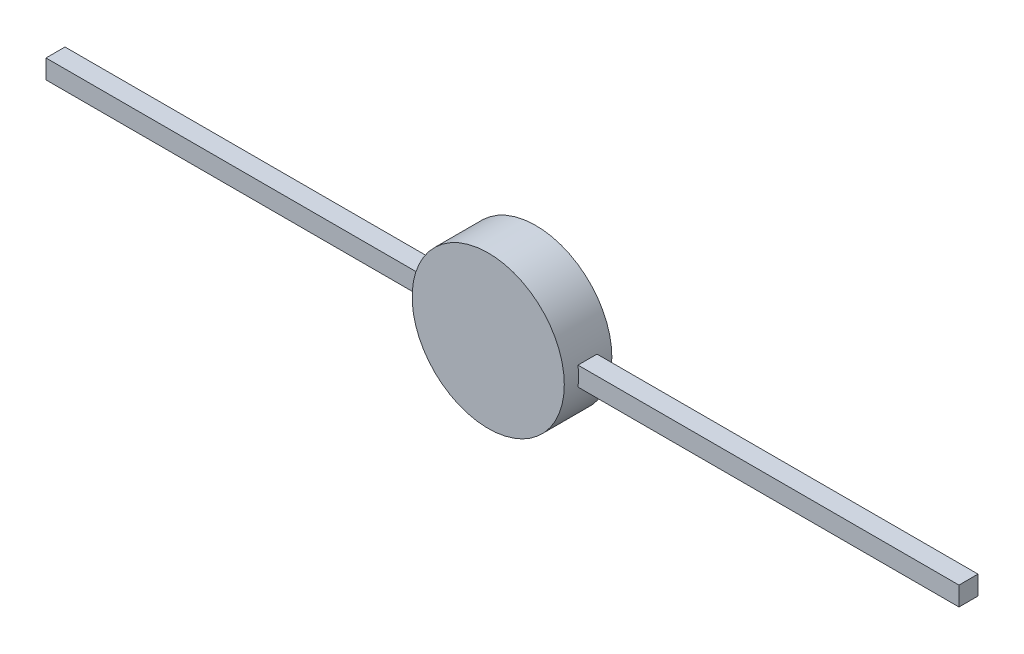
SolidWorks part; units mm, degrees
material "PVC Rigid"
ref_plane "Front Plane" through (0, 0, 0) normal (0, 0, 1) x (1, 0, 0)
ref_plane "Top Plane" through (0, 0, 0) normal (0, 1, 0) x (1, 0, 0)
ref_plane "Right Plane" through (0, 0, 0) normal (1, 0, 0) x (0, 0, -1)
sketch "Sketch1" plane through (0, 0, 0) normal (0, 0, 1) x (1, 0, 0)
  circle A0 centre (0, 0) radius 8
extrude "Boss-Extrude1" add sketch "Sketch1" along normal blind 5 contours A0
ref_plane "Plane1" through (-48, 0, 0) normal (-1, 0, 0) x (0, 0, 1)
sketch "Sketch2" plane through (-48, 0, 0) normal (-1, 0, 0) x (0, 0, 1)
  line L0 (0, 0) -> (5, 0) construction
  line L1 (5, -8) -> (5, 8) construction
  line L3 (1.5, -1) -> (3.5, -1)
  line L4 (1.5, -1) -> (1.5, 1)
  line L5 (1.5, 1) -> (3.5, 1)
  line L6 (3.5, -1) -> (3.5, 1)
  line L7 (1.5, -1) -> (3.5, 1) construction
  line L8 (1.5, 1) -> (3.5, -1) construction
  point P5 (2.5, 0)
  point P6 (2.5, 0)
extrude "Boss-Extrude2" add sketch "Sketch2" against normal blind 48
mirror "Mirror1" about plane through (0, 0, 0) normal (1, 0, 0) of "Boss-Extrude2"
